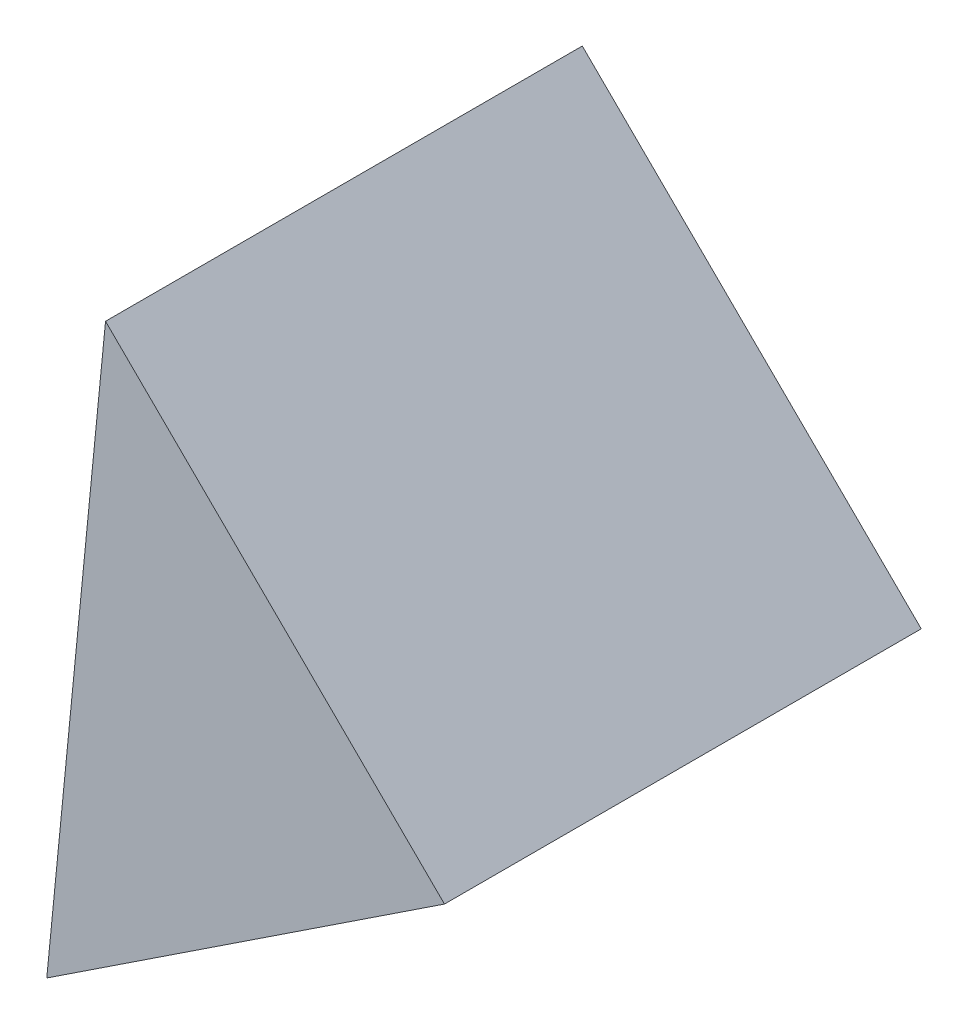
SolidWorks part; units mm, degrees
ref_plane "前视基准面" through (0, 0, 0) normal (0, 0, 1) x (1, 0, 0)
ref_plane "上视基准面" through (0, 0, 0) normal (0, 1, 0) x (1, 0, 0)
ref_plane "右视基准面" through (0, 0, 0) normal (1, 0, 0) x (0, 0, -1)
sketch "草图2" plane through (0, 0, 0) normal (0, 0, 1) x (1, 0, 0)
  line L0 (21.5422, 14.6325) -> (3.7679, 32.213)
  line L1 (21.5422, 14.6325) -> (0.6862, 0.8475)
  line L2 (0.6862, 0.8475) -> (3.7679, 32.213)
  dimension "D1" = 25
  dimension "D2" = 25
extrude "凸台-拉伸1" add sketch "草图2" along normal blind 25
